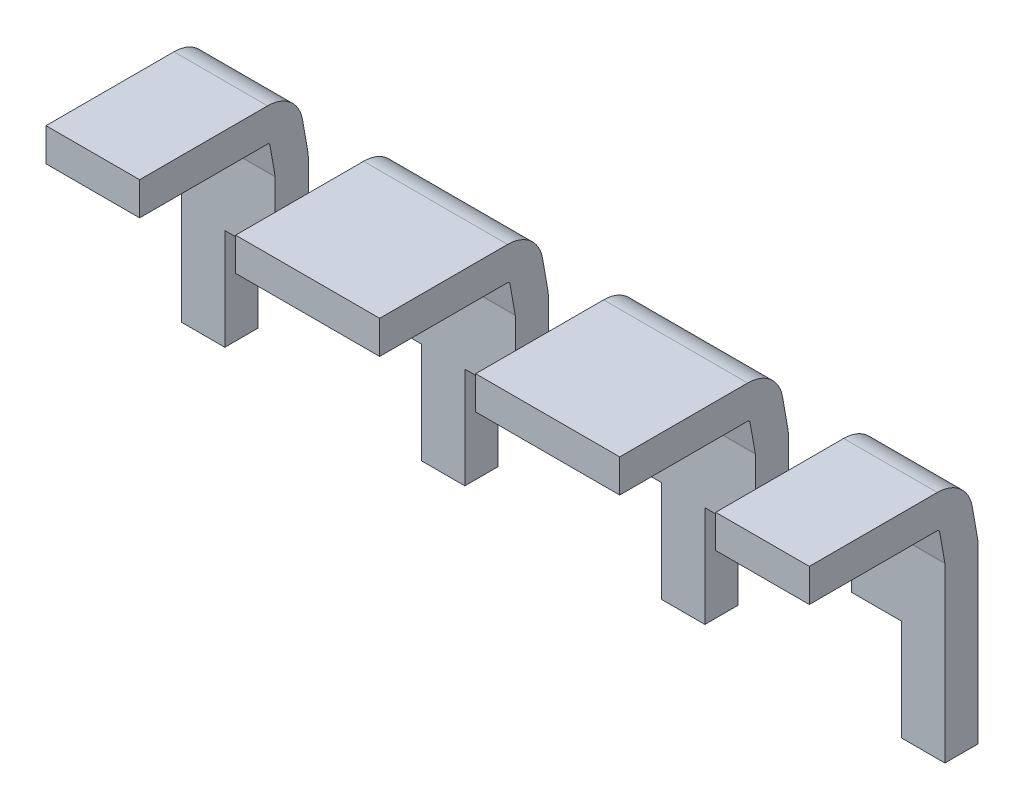
SolidWorks part; units mm, degrees
ref_plane "Front Plane" through (0, 0, 0) normal (0, 0, 1) x (1, 0, 0)
ref_plane "Top Plane" through (0, 0, 0) normal (0, 1, 0) x (1, 0, 0)
ref_plane "Right Plane" through (0, 0, 0) normal (1, 0, 0) x (0, 0, -1)
sketch "Sketch1" plane through (0, 0, 0) normal (0, 0, 1) x (1, 0, 0)
  line L0 (3.048, 0.175) -> (4.572, 0.175) construction
  line L1 (-2.032, 0.175) -> (-0.508, 0.175)
  line L2 (-2.032, 0.175) -> (-2.032, -0.175)
  line L3 (-2.032, -0.175) -> (-0.508, -0.175)
  line L4 (-0.508, 0.175) -> (-0.508, -0.175)
  line L5 (-2.032, 0.175) -> (-0.508, -0.175) construction
  line L6 (-2.032, -0.175) -> (-0.508, 0.175) construction
  line L7 (0.508, 0.175) -> (2.032, 0.175)
  line L8 (0.508, 0.175) -> (0.508, -0.175)
  line L9 (0.508, -0.175) -> (2.032, -0.175)
  line L10 (2.032, 0.175) -> (2.032, -0.175)
  line L11 (0.508, 0.175) -> (2.032, -0.175) construction
  line L12 (0.508, -0.175) -> (2.032, 0.175) construction
  line L13 (3.048, 0.175) -> (3.048, -0.175)
  line L14 (3.048, -0.175) -> (4.572, -0.175) construction
  line L15 (4.572, 0.175) -> (4.572, -0.175) construction
  line L16 (3.048, 0.175) -> (4.572, -0.175) construction
  line L17 (3.048, -0.175) -> (4.572, 0.175) construction
  line L18 (-4.572, 0.175) -> (-3.048, 0.175) construction
  line L19 (-4.572, 0.175) -> (-4.572, -0.175) construction
  line L20 (-4.572, -0.175) -> (-3.048, -0.175) construction
  line L21 (-3.048, 0.175) -> (-3.048, -0.175)
  line L22 (-4.572, 0.175) -> (-3.048, -0.175) construction
  line L23 (-4.572, -0.175) -> (-3.048, 0.175) construction
  line L24 (-4.0386, 0.175) -> (-4.0386, -0.175)
  line L25 (4.0386, 0.175) -> (4.0386, -0.175)
  line L26 (4.0386, 0.175) -> (3.048, 0.175)
  line L27 (4.0386, -0.175) -> (3.048, -0.175)
  line L28 (-3.048, 0.175) -> (-4.0386, 0.175)
  line L29 (-3.048, -0.175) -> (-4.0386, -0.175)
  point P0 (-1.27, 0)
  point P5 (1.27, 0)
  point P12 (3.81, 0)
  point P17 (-3.81, 0)
  dimension "D1" = 1.524
  dimension "D2" = 2.54
  dimension "D3" = 1.524
  dimension "D4" = 1.27
  dimension "D5" = 0.35
  dimension "D6" = 0.5334
  dimension "D7" = 0.5334
  dimension "D8" = 2.54
  dimension "D9" = 2.54
sketch "Sketch2" plane through (0, 0, 0) normal (1, 0, 0) x (0, 0, -1)
  line L0 (0, 0) -> (1.354, 0)
  line L1 (1.61, -0.5175) -> (1.61, -2.345)
  line L2 (1.607, -0.4828) -> (1.551, -0.1653)
  arc A0 (1.354, 0) -> (1.551, -0.1653) centre (1.354, -0.2) cw
  arc A1 (1.607, -0.4828) -> (1.61, -0.5175) centre (1.41, -0.5175) cw
  point P10 (1.61, -0.5)
  dimension "D5" = 0.2
  dimension "D6" = 0.2
  dimension "D1" = 1.61
  dimension "D2" = 10
  dimension "D3" = 1.845
  dimension "D4" = 0.5
sweep "Sweep11" add profiles "Sketch1" path "Sketch2"
sketch "Sketch10" plane through (0, 0.2906, -1.6483) normal (0, 0.1736, -0.9848) x (-1, 0, 0)
  line L0 (-4.0386, -0.7545) -> (-3.048, -0.7545) construction
  line L1 (-3.5814, -1.5045) -> (-3.048, -1.5045)
  line L2 (-3.5814, -1.5045) -> (-3.5814, -2.6193)
  line L3 (-3.5814, -2.6193) -> (-3.048, -2.6193)
  line L4 (-3.048, -1.5045) -> (-3.048, -2.6193)
  line L5 (-3.5814, -1.5045) -> (-3.048, -2.6193) construction
  line L6 (-3.5814, -2.6193) -> (-3.048, -1.5045) construction
  line L8 (-2.032, -1.5045) -> (-1.4986, -1.5045)
  line L9 (-2.032, -1.5045) -> (-2.032, -2.6193)
  line L10 (-2.032, -2.6193) -> (-1.4986, -2.6193)
  line L11 (-0.508, -1.5045) -> (-0.508, -2.6193)
  line L12 (-2.032, -1.5045) -> (-0.508, -2.6193) construction
  line L13 (-2.032, -2.6193) -> (-0.508, -1.5045) construction
  line L14 (0.508, -1.5045) -> (1.0414, -1.5045)
  line L15 (0.508, -1.5045) -> (0.508, -2.6193)
  line L16 (0.508, -2.6193) -> (1.0414, -2.6193)
  line L17 (2.032, -1.5045) -> (2.032, -2.6193)
  line L18 (0.508, -1.5045) -> (2.032, -2.6193) construction
  line L19 (0.508, -2.6193) -> (2.032, -1.5045) construction
  line L20 (3.5814, -1.5045) -> (3.048, -1.5045)
  line L21 (3.5814, -1.5045) -> (3.5814, -2.6193)
  line L22 (3.5814, -2.6193) -> (3.048, -2.6193)
  line L23 (3.048, -1.5045) -> (3.048, -2.6193)
  line L24 (3.5814, -1.5045) -> (3.048, -2.6193) construction
  line L25 (3.5814, -2.6193) -> (3.048, -1.5045) construction
  line L28 (-2.032, -0.8196) -> (-2.032, -2.6193) construction
  line L29 (0.508, -0.8196) -> (0.508, -2.6193) construction
  line L32 (-1.4986, -1.5045) -> (-1.4986, -2.6193)
  line L33 (-1.0414, -1.5045) -> (-1.0414, -2.6193)
  line L34 (1.0414, -1.5045) -> (1.0414, -2.6193)
  line L35 (1.4986, -1.5045) -> (1.4986, -2.6193)
  line L36 (-1.0414, -1.5045) -> (-0.508, -1.5045)
  line L37 (-1.0414, -2.6193) -> (-0.508, -2.6193)
  line L38 (1.4986, -1.5045) -> (2.032, -1.5045)
  line L39 (1.4986, -2.6193) -> (2.032, -2.6193)
  line L41 (-3.048, -0.8196) -> (-3.048, -2.6193) construction
  line L42 (3.048, -0.8196) -> (3.048, -2.6193) construction
  line L43 (3.048, -2.6193) -> (4.0386, -2.6193) construction
  line L44 (-4.0386, -2.6193) -> (-3.048, -2.6193) construction
  point P0 (-3.3147, -2.0619)
  point P6 (-1.27, -2.0619)
  point P15 (1.27, -2.0619)
  point P21 (3.3147, -2.0619)
  dimension "D1" = 0.5334
  dimension "D2" = 0.5334
  dimension "D3" = 0.4572
  dimension "D4" = 0.4572
  dimension "D5" = 0.2286
  dimension "D6" = 0.2286
  dimension "D7" = 0.75
extrude "Extrude1" cut sketch "Sketch10" against normal through all
